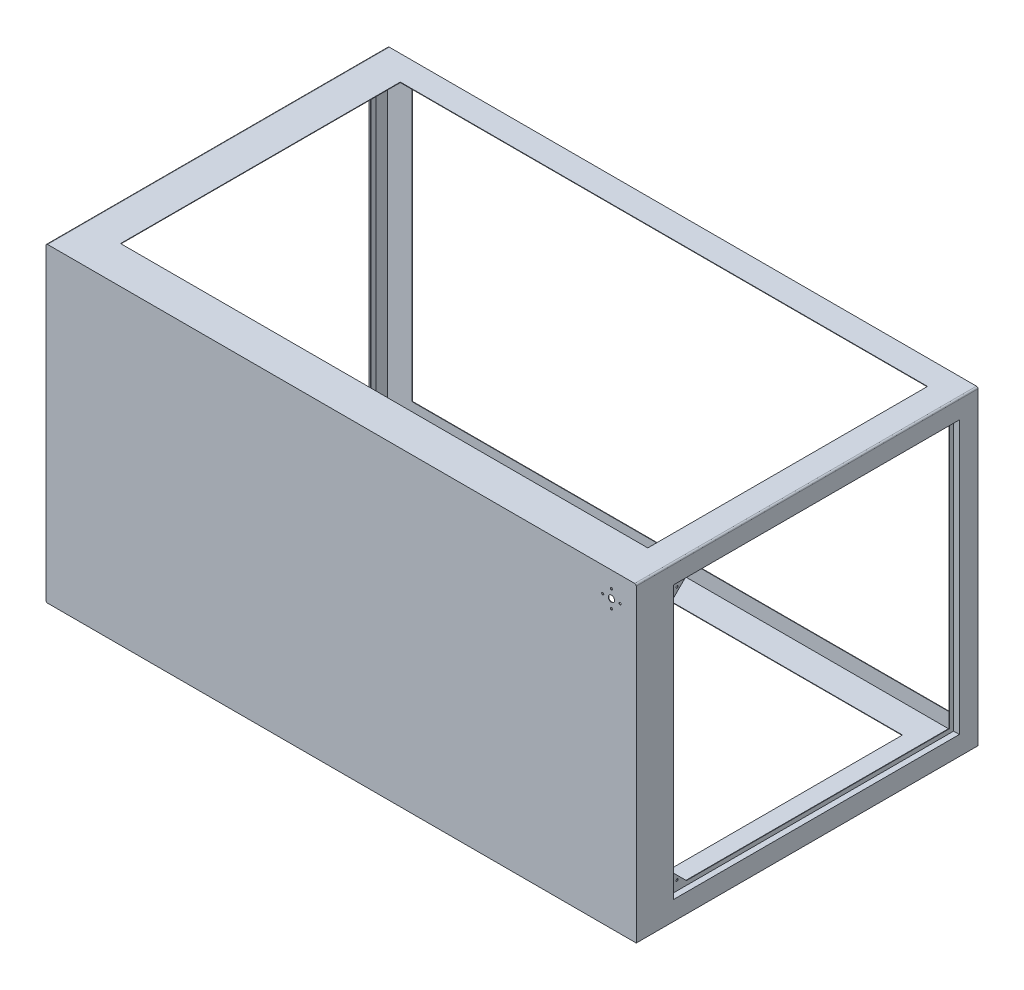
SolidWorks part; units mm, degrees
ref_plane "前视基准面" through (0, 0, 0) normal (0, 0, 1) x (1, 0, 0)
ref_plane "上视基准面" through (0, 0, 0) normal (0, 1, 0) x (1, 0, 0)
ref_plane "右视基准面" through (0, 0, 0) normal (1, 0, 0) x (0, 0, -1)
sketch "草图1" plane through (0, 0, 0) normal (0, 0, 1) x (1, 0, 0)
  line L1 (950, -500) -> (-950, -500)
  line L2 (950, -500) -> (950, 500)
  line L3 (950, 500) -> (-950, 500)
  line L4 (-950, -500) -> (-950, 500)
  line L5 (950, -500) -> (-950, 500) construction
  line L6 (950, 500) -> (-950, -500) construction
  point P0 (0, 0)
  dimension "D1" = 1900
  dimension "D2" = 1000
extrude "凸台-拉伸1" add sketch "草图1" along normal mid plane 1100
shell "抽壳1" thickness 1.5
sketch "草图2" plane through (0, 0, -550) normal (0, 0, -1) x (-1, 0, 0)
  line L0 (950, 500) -> (950, -500) construction
  line L1 (-870, 450) -> (870, 450)
  line L2 (-870, 450) -> (-870, -450)
  line L3 (-870, -450) -> (870, -450)
  line L4 (870, 450) -> (870, -450)
  line L5 (-870, 450) -> (870, -450) construction
  line L6 (-870, -450) -> (870, 450) construction
  line L7 (950, -500) -> (-950, -500) construction
  line L9 (948.5, -498.5) -> (-948.5, -498.5)
  line L10 (948.5, -498.5) -> (948.5, 498.5)
  line L11 (948.5, 498.5) -> (-948.5, 498.5)
  line L12 (-948.5, -498.5) -> (-948.5, 498.5)
  line L13 (948.5, -498.5) -> (-948.5, 498.5) construction
  line L14 (948.5, 498.5) -> (-948.5, -498.5) construction
  point P0 (0, 0)
  point P10 (0, 0)
  dimension "D1" = 80
  dimension "D2" = 50
extrude "凸台-拉伸2" add sketch "草图2" against normal blind 1.5 separate body
fillet "圆角1" radius 5 4 edges at (-950, 500, 0) (-950, -500, 0) (948.5, -498.5, -0.75) (950, 500, 0)
sketch "草图9" plane through (0, 0, 550) normal (0, 0, 1) x (1, 0, 0)
  line L0 (950, -500) -> (950, 495) construction
  line L2 (945, 500) -> (-945, 500) construction
  circle A0 centre (870, 420) radius 10
  dimension "D1" = 20
  dimension "D2" = 80
  dimension "D3" = 80
extrude "切除-拉伸3" cut sketch "草图9" against normal blind 10
sketch "草图10" plane through (0, 500, 0) normal (0, 1, 0) x (1, 0, 0)
  line L1 (867.0784, -430) -> (-830, -430)
  line L2 (867.0784, -430) -> (867.0784, 470.514)
  line L3 (867.0784, 470.514) -> (-830, 470.514)
  line L4 (-830, -430) -> (-830, 470.514)
  line L5 (945, 550) -> (-945, 550) construction
  line L7 (945, -550) -> (-945, -550) construction
  line L8 (0, -550) -> (0, 550) construction
  line L9 (-950, -550) -> (-950, 550) construction
  dimension "D1" = 120
extrude "切除-拉伸4" cut sketch "草图10" against normal blind 20
sketch "草图18" plane through (-950, 0, 0) normal (-1, 0, 0) x (0, 0, 1)
  line L0 (-550, 498.5) -> (-550, -498.5) construction
  line L1 (430, 438.5) -> (-490, 438.5)
  line L2 (430, 438.5) -> (430, -438.5)
  line L3 (430, -438.5) -> (-490, -438.5)
  line L4 (-490, 438.5) -> (-490, -438.5)
  line L7 (550, 495) -> (550, -495) construction
  line L8 (-550, 0) -> (550, 0) construction
  line L9 (-550, 495) -> (-550, -495) construction
  line L10 (548.5, 498.5) -> (-550, 498.5) construction
  dimension "D1" = 60
  dimension "D2" = 60
  dimension "D4" = 120
extrude "切除-拉伸5" cut sketch "草图18" against normal blind 1.5
sketch "草图34" plane through (-948.5, 0, 0) normal (1, 0, 0) x (0, 0, -1)
  line L1 (-430, -438.5) -> (490, -438.5)
  line L2 (-430, -438.5) -> (-430, 438.5)
  line L3 (-430, 438.5) -> (490, 438.5)
  line L4 (490, -438.5) -> (490, 438.5)
  line L5 (491.5, 440) -> (-431.5, 440)
  line L6 (491.5, 440) -> (491.5, -440)
  line L7 (491.5, -440) -> (-431.5, -440)
  line L8 (-431.5, 440) -> (-431.5, -440)
  dimension "D1" = 1.5
  dimension "D2" = 1.5
  dimension "D3" = 1.5
  dimension "D4" = 1.5
extrude "凸台-拉伸6" add sketch "草图34" along normal blind 17
sketch "草图35" plane through (-931.5, 0, 0) normal (1, 0, 0) x (0, 0, -1)
  line L1 (491.5, 440) -> (-431.5, 440)
  line L2 (491.5, 440) -> (491.5, -440)
  line L3 (491.5, -440) -> (-431.5, -440)
  line L4 (-431.5, 440) -> (-431.5, -440)
  line L5 (-416.5, -425) -> (476.5, -425)
  line L6 (-416.5, -425) -> (-416.5, 425)
  line L7 (-416.5, 425) -> (476.5, 425)
  line L8 (476.5, -425) -> (476.5, 425)
  dimension "D1" = 15
  dimension "D2" = 15
  dimension "D3" = 15
  dimension "D4" = 15
extrude "凸台-拉伸7" add sketch "草图35" along normal blind 1.5
sketch "草图36" plane through (-931.5, 0, 0) normal (-1, 0, 0) x (0, 0, 1)
  line L0 (370, 425) -> (416.5, 378.5)
  line L1 (-476.5, 425) -> (416.5, 425) construction
  line L2 (416.5, 425) -> (416.5, -425) construction
  line L3 (416.5, 378.5) -> (416.5, 425)
  line L4 (416.5, 425) -> (370, 425)
  line L5 (-490, 438.5) -> (430, 438.5) construction
  line L6 (430, -438.5) -> (430, 438.5) construction
  line L7 (416.5, -378.5) -> (370, -425)
  line L8 (370, -425) -> (416.5, -425)
  line L9 (416.5, -425) -> (416.5, -378.5)
  line L10 (-490, -438.5) -> (430, -438.5) construction
  dimension "D1" = 60
  dimension "D2" = 60
  dimension "D3" = 60
  dimension "D4" = 60
extrude "凸台-拉伸8" add sketch "草图36" against normal blind 1.5
hole_wizard "Ø7.0 (7) 直径孔1" positions "草图38" profile "草图37" hole size "Ø7.0" standard "GB"
sketch "草图38" plane through (-931.5, 0, 0) normal (-1, 0, 0) x (0, 0, 1)
  line L0 (430, 438.5) -> (430, -438.5) construction
  line L1 (-490, 438.5) -> (430, 438.5) construction
  line L2 (430, -438.5) -> (-490, -438.5) construction
  point P0 (400, 408.5)
  point P2 (400, -408.5)
  dimension "D1" = 30
  dimension "D2" = 30
  dimension "D3" = 30
  dimension "D4" = 30
sketch "草图37" plane through (-931.5, 408.5, 400) normal (0, 1, 0) x (0, 0, 1)
  line L0 (0, 0) -> (0, 3.603)
  line L1 (0, 3.603) -> (3.5, 1.5)
  line L2 (3.5, 1.5) -> (3.5, 0)
  line L5 (3.5, 0) -> (0, 0)
  line L10 (0, 3.603) -> (-3.5, 1.5) construction
  line L11 (0, -6.35) -> (0, 107.95) construction
  dimension "孔直径" = 7
  dimension "孔深度" = 1.5
  dimension "导头角度" = 118
mirror "镜向4" about plane through (0, 0, 0) normal (1, 0, 0) of "切除-拉伸5"
mirror "镜向7" about plane through (0, 0, 0) normal (1, 0, 0) of "凸台-拉伸6"
mirror "镜向8" about plane through (0, 0, 0) normal (1, 0, 0) of "凸台-拉伸7"
mirror "镜向10" about plane through (0, 0, 0) normal (1, 0, 0) of "凸台-拉伸8"
mirror "镜向11" about plane through (0, 0, 0) normal (1, 0, 0) of "Ø7.0 (7) 直径孔1"
sketch "草图53" plane through (0, 0, 548.5) normal (0, 0, -1) x (-1, 0, 0)
  line L0 (850, -445) -> (850, -453)
  line L1 (945, -500) -> (-950, -500) construction
  line L2 (852, -455) -> (872, -455)
  line L3 (874, -453) -> (874, -445)
  line L4 (874, -445) -> (872.5, -445)
  line L5 (872.5, -445) -> (872.5, -452)
  line L6 (871, -453.5) -> (853, -453.5)
  line L7 (851.5, -452) -> (851.5, -445)
  line L8 (851.5, -445) -> (850, -445)
  line L10 (950, 495) -> (950, -495) construction
  arc A0 (872, -455) -> (874, -453) centre (872, -453) ccw
  arc A1 (850, -453) -> (852, -455) centre (852, -453) ccw
  arc A2 (872.5, -452) -> (871, -453.5) centre (871, -452) cw
  arc A3 (853, -453.5) -> (851.5, -452) centre (853, -452) cw
  point P14 (874, -455)
  dimension "D8" = 2
  dimension "D9" = 1.5
  dimension "D1" = 1.5
  dimension "D2" = 1.5
  dimension "D3" = 1.5
  dimension "D4" = 45
  dimension "D5" = 24
  dimension "D6" = 55
  dimension "D7" = 100
  dimension "D10" = 55
extrude "凸台-拉伸9" add sketch "草图53" along normal blind 897
sketch "草图54" plane through (0, 0, 548.5) normal (0, 0, -1) x (-1, 0, 0)
  line L0 (927, -399) -> (927, -417)
  line L1 (925, -419) -> (874, -419)
  line L2 (872, -417) -> (872, -399)
  line L3 (872, -399) -> (873.5, -399)
  line L4 (873.5, -399) -> (873.5, -416)
  line L5 (875, -417.5) -> (924, -417.5)
  line L6 (925.5, -416) -> (925.5, -399)
  line L7 (925.5, -399) -> (927, -399)
  line L8 (948.5, 498.5) -> (948.5, -498.5) construction
  line L9 (945, -500) -> (-950, -500) construction
  line L10 (950, 495) -> (950, -495) construction
  arc A0 (927, -417) -> (925, -419) centre (925, -417) cw
  arc A1 (874, -419) -> (872, -417) centre (874, -417) cw
  arc A2 (924, -417.5) -> (925.5, -416) centre (924, -416) ccw
  arc A3 (873.5, -416) -> (875, -417.5) centre (875, -416) ccw
  point P16 (927, -419)
  point P19 (872, -419)
  dimension "D9" = 2
  dimension "D10" = 1.5
  dimension "D1" = 81
  dimension "D2" = 1.5
  dimension "D3" = 1.5
  dimension "D4" = 1.5
  dimension "D5" = 20
  dimension "D6" = 20
  dimension "D7" = 23
  dimension "D8" = 55
extrude "凸台-拉伸10" add sketch "草图54" along normal blind 897
hole_wizard "Ø7.0 (7) 直径孔3" positions "草图57" profile "草图56" hole size "Ø7.0" standard "GB"
sketch "草图57" plane through (0, 0, 550) normal (0, 0, 1) x (1, 0, 0)
  circle A0 centre (870, 420) radius 10 construction
  point P0 (870, 392)
  dimension "D2" = 0
  dimension "D1" = 28
sketch "草图56" plane through (870, 392, 550) normal (1, 0, 0) x (0, -1, 0)
  line L0 (0, 0) -> (0, 4.103)
  line L1 (0, 4.103) -> (3.5, 2)
  line L2 (3.5, 2) -> (3.5, 0)
  line L5 (3.5, 0) -> (0, 0)
  line L10 (0, 4.103) -> (-3.5, 2) construction
  line L11 (0, -6.35) -> (0, 107.95) construction
  dimension "孔直径" = 7
  dimension "孔深度" = 2
  dimension "导头角度" = 118
pattern_circular "阵列(圆周)2" count 4 over 360 about axis through (870, 420, 0) along (0, 0, 1) of "Ø7.0 (7) 直径孔3"
sketch "草图60" plane through (0, 0, -550) normal (0, 0, -1) x (-1, 0, 0)
  line L0 (950, 495) -> (950, -495) construction
  line L1 (-910, 470) -> (910, 470)
  line L2 (-910, 470) -> (-910, -465)
  line L3 (-910, -465) -> (910, -465)
  line L4 (910, 470) -> (910, -465)
  line L5 (945, -500) -> (-950, -500) construction
  line L6 (-950, -500) -> (-950, 495) construction
  line L7 (-945, 500) -> (945, 500) construction
  dimension "D1" = 40
  dimension "D2" = 35
  dimension "D3" = 40
  dimension "D4" = 30
sketch "草图84" plane through (0, -500, 0) normal (0, -1, 0) x (1, 0, 0)
  line L0 (-945, 550) -> (950, 550) construction
  line L1 (800, -456.8935) -> (-795.1416, -456.8935)
  line L2 (800, -456.8935) -> (800, 430)
  line L3 (800, 430) -> (-795.1416, 430)
  line L4 (-795.1416, -456.8935) -> (-795.1416, 430)
  line L5 (800, -456.8935) -> (-795.1416, 430) construction
  line L6 (800, 430) -> (-795.1416, -456.8935) construction
  line L7 (950, 550) -> (950, -550) construction
  point P0 (210.2138, -128.9743)
  dimension "D1" = 120
  dimension "D2" = 150
extrude "切除-拉伸22" cut sketch "草图84" against normal blind 10
